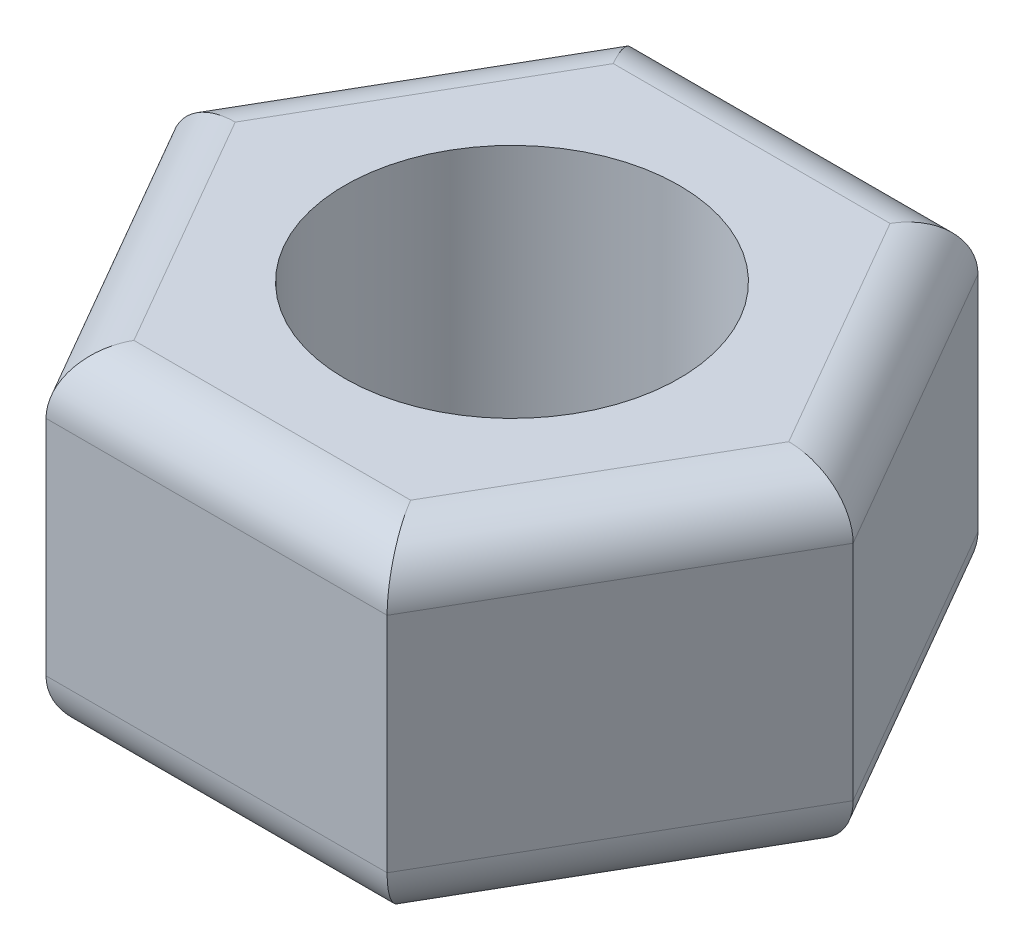
SolidWorks part; units mm, degrees
ref_plane "前视基准面" through (0, 0, 0) normal (0, 0, 1) x (1, 0, 0)
ref_plane "上视基准面" through (0, 0, 0) normal (0, 1, 0) x (1, 0, 0)
ref_plane "右视基准面" through (0, 0, 0) normal (1, 0, 0) x (0, 0, -1)
sketch "草图1" plane through (0, 0, 0) normal (0, 1, 0) x (1, 0, 0)
  line L1 (3.06, 0) -> (1.53, 2.65)
  line L2 (1.53, 2.65) -> (-1.53, 2.65)
  line L3 (-1.53, 2.65) -> (-3.06, 0)
  line L4 (-3.06, 0) -> (-1.53, -2.65)
  line L5 (-1.53, -2.65) -> (1.53, -2.65)
  line L6 (1.53, -2.65) -> (3.06, 0)
  circle A0 centre (0, 0) radius 2.65 construction
  dimension "D1" = 5.3
extrude "凸台-拉伸1" add sketch "草图1" along normal blind 3
sketch "草图2" plane through (0, 3, 0) normal (0, 1, 0) x (1, 0, 0)
  circle A0 centre (0, 0) radius 1.5
  dimension "D1" = 3
extrude "切除-拉伸1" cut sketch "草图2" against normal blind 3
fillet "圆角1" radius 0.5 12 edges at (-2.295, 0, -1.325) (-2.295, 0, 1.325) (0, 0, 2.65) (2.295, 0, 1.325) (2.295, 0, -1.325) (0, 0, -2.65) (0, 3, -2.65) (-2.295, 3, -1.325) (-2.295, 3, 1.325) (0, 3, 2.65) (2.295, 3, 1.325) (2.295, 3, -1.325)
